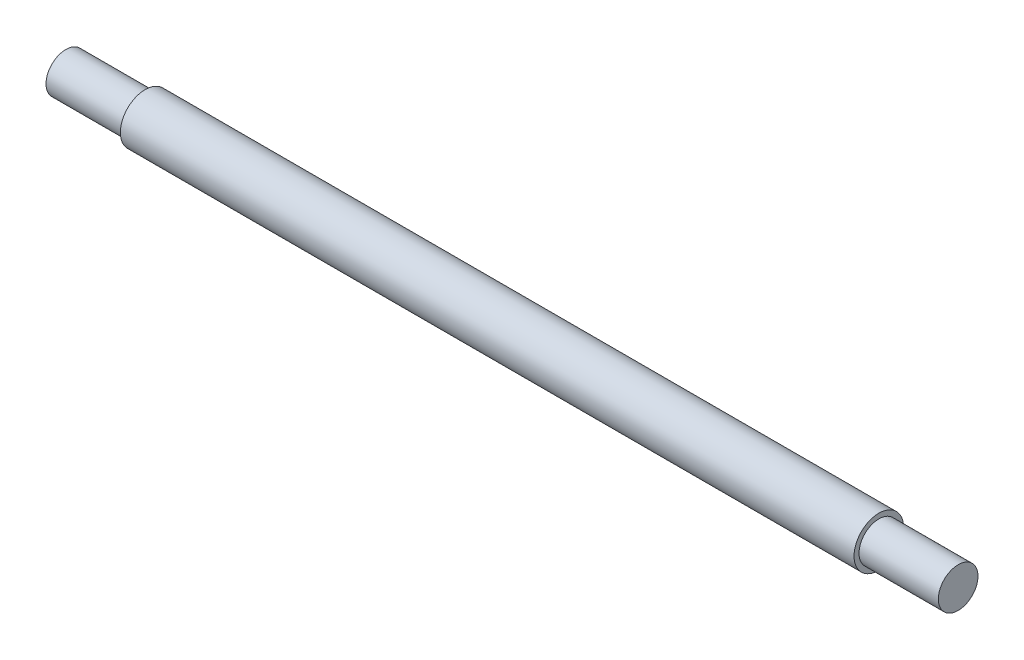
SolidWorks part; units mm, degrees
ref_plane "Front Plane" through (0, 0, 0) normal (0, 0, 1) x (1, 0, 0)
ref_plane "Top Plane" through (0, 0, 0) normal (0, 1, 0) x (1, 0, 0)
ref_plane "Right Plane" through (0, 0, 0) normal (1, 0, 0) x (0, 0, -1)
sketch "Sketch1" plane through (0, 0, 0) normal (1, 0, 0) x (0, 0, -1)
  circle A0 centre (0, 0) radius 2.5
  dimension "D1" = 5
extrude "Boss-Extrude1" add sketch "Sketch1" along normal mid plane 90
sketch "Sketch2" plane through (45, 0, 0) normal (1, 0, 0) x (0, 0, -1)
  circle A0 centre (0, 0) radius 2
  circle A1 centre (0, 0) radius 2.5
  dimension "D1" = 4
extrude "Cut-Extrude1" cut sketch "Sketch2" against normal blind 8
sketch "Sketch3" plane through (-45, 0, 0) normal (-1, 0, 0) x (0, 0, 1)
  circle A0 centre (0, 0) radius 2
  circle A1 centre (0, 0) radius 2.5
  dimension "D1" = 4
extrude "Cut-Extrude2" cut sketch "Sketch3" against normal blind 8
